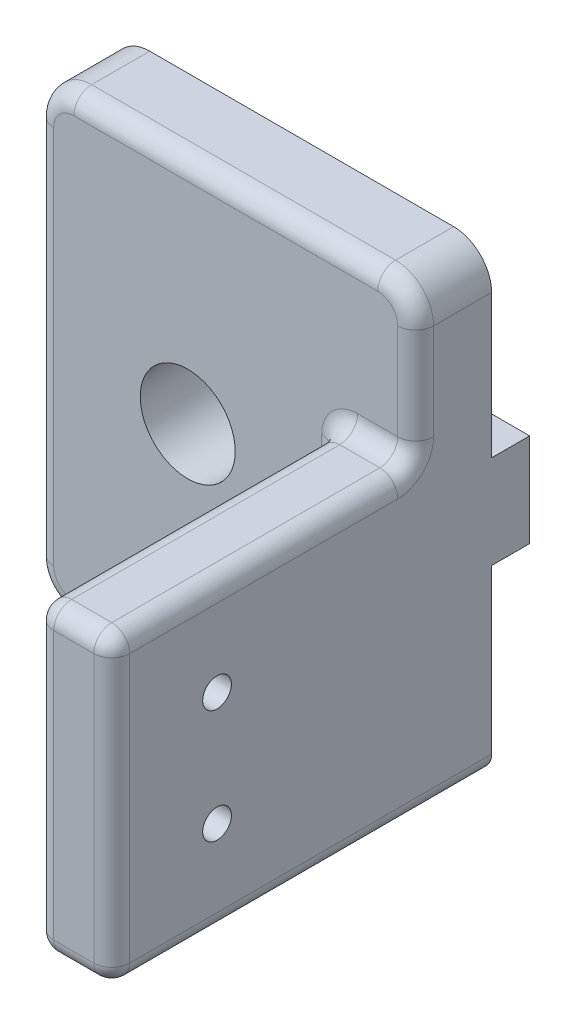
SolidWorks part; units mm, degrees
ref_plane "Front Plane" through (0, 0, 0) normal (0, 0, 1) x (1, 0, 0)
ref_plane "Top Plane" through (0, 0, 0) normal (0, 1, 0) x (1, 0, 0)
ref_plane "Right Plane" through (0, 0, 0) normal (1, 0, 0) x (0, 0, -1)
sketch "Sketch1" plane through (0, 0, 0) normal (0, 0, 1) x (1, 0, 0)
  line L1 (0, 0) -> (31.75, 0)
  line L2 (0, 0) -> (0, 38.1)
  line L3 (0, 38.1) -> (31.75, 38.1)
  line L4 (31.75, 0) -> (31.75, 38.1)
  line L5 (0, 0) -> (31.75, 38.1) construction
  line L6 (0, 38.1) -> (31.75, 0) construction
  point P4 (15.875, 19.05)
  dimension "D1" = 31.75
  dimension "D2" = 38.1
extrude "Boss-Extrude1" add sketch "Sketch1" along normal blind 6.35 contours L2 L3 L4 L1
sketch "Sketch2" plane through (0, 0, 6.35) normal (0, 0, 1) x (1, 0, 0)
  line L0 (15.875, 38.1) -> (15.875, 0) construction
  line L1 (0, 38.1) -> (31.75, 38.1) construction
  line L2 (0, 0) -> (31.75, 0) construction
  line L3 (0, 0) -> (0, 38.1) construction
  line L8 (31.75, 0) -> (25.4, 0)
  line L9 (31.75, 0) -> (31.75, 25.4)
  line L10 (31.75, 25.4) -> (25.4, 25.4)
  line L11 (25.4, 0) -> (25.4, 25.4)
  line L12 (31.75, 0) -> (25.4, 25.4) construction
  line L13 (31.75, 25.4) -> (25.4, 0) construction
  circle A0 centre (12.7, 19.05) radius 3.9688 construction
  point P8 (28.575, 17.45)
  point P13 (28.575, 12.7)
  point P18 (28.575, 7.95)
  dimension "D2" = 7.9375
  dimension "D1" = 19.05
  dimension "D3" = 25.4
  dimension "D4" = 12.7
  dimension "D5" = 6.35
  dimension "D6" = 7.95
  dimension "D7" = 9.5
extrude "Boss-Extrude2" add sketch "Sketch2" along normal blind 25.4 contours L11 L10 L9 L8
sketch "Sketch3" plane through (25.4, 0, 0) normal (-1, 0, 0) x (0, 0, 1)
  line L0 (31.75, 0) -> (6.35, 0) construction
  line L1 (31.75, 0) -> (31.75, 25.4) construction
  circle A0 centre (22.95, 17.45) radius 1.2
  circle A1 centre (22.95, 7.95) radius 1.2
  dimension "D2" = 2.4
  dimension "D1" = 9.5
  dimension "D3" = 7.95
  dimension "D4" = 8.8
extrude "Cut-Extrude1" cut sketch "Sketch3" against normal through all contours A0
sketch "Sketch4" plane through (0, 0, 6.35) normal (0, 0, 1) x (1, 0, 0)
  line L0 (0, 0) -> (0, 38.1) construction
  line L1 (0, 0) -> (25.4, 0) construction
  circle A0 centre (12.7, 19.05) radius 3.9688
  dimension "D1" = 7.9375
  dimension "D2" = 12.7
  dimension "D3" = 19.05
extrude "Cut-Extrude2" cut sketch "Sketch4" against normal through all
sketch "Sketch5" plane through (0, 0, 0) normal (-1, 0, 0) x (0, 0, 1)
  line L0 (0, 0) -> (0, 38.1) construction
  line L1 (0, 0) -> (0, 38.1)
  line L3 (0, 22.95) -> (-3.18, 22.95)
  line L4 (0, 22.95) -> (0, 15.15)
  line L5 (0, 15.15) -> (-3.18, 15.15)
  line L6 (-3.18, 22.95) -> (-3.18, 15.15)
  line L7 (0, 22.95) -> (-3.18, 15.15) construction
  line L8 (0, 15.15) -> (-3.18, 22.95) construction
  point P6 (-1.59, 19.05)
  dimension "D1" = 7.8
  dimension "D2" = 3.18
  dimension "D3" = 19.05
extrude "Boss-Extrude3" add sketch "Sketch5" against normal up to surface (31.75 mm away) contours L3 L6 L5 L1 up to face at (31.75, 17.45, 24.15)
fillet "Fillet1" radius 3.175 3 edges at (31.75, 38.1, 3.175) (0, 38.1, 3.175) (0, 0, 3.175)
fillet "Fillet2" radius 1.5 17 edges at (25.4, 0, 19.05) (14.2875, 0, 6.35) (0.9299, 0.9299, 6.35) (0, 19.05, 6.35) (0.9299, 37.1701, 6.35) (15.875, 38.1, 6.35) (30.8201, 37.1701, 6.35) (31.75, 30.1625, 6.35) (28.575, 25.4, 6.35) (25.4, 12.7, 31.75) (31.75, 12.7, 31.75) (31.75, 0, 15.875) (28.575, 0, 31.75) (25.4, 12.7, 6.35) (28.575, 25.4, 31.75) (31.75, 25.4, 19.05) (25.4, 25.4, 19.05)
sketch "Sketch6" plane through (0, 0, 0) normal (0, 0, 1) x (1, 0, 0)
  line L2 (13.4355, 22.95) -> (11.9645, 22.95)
  line L3 (11.9645, 15.15) -> (13.4355, 15.15)
  line L4 (13.4355, 22.95) -> (11.9645, 22.95)
  line L5 (11.9645, 15.15) -> (13.4355, 15.15)
  arc A2 (11.9645, 22.95) -> (11.9645, 15.15) centre (12.7, 19.05) ccw
  arc A3 (13.4355, 15.15) -> (13.4355, 22.95) centre (12.7, 19.05) ccw
  arc A4 (11.9645, 22.95) -> (11.9645, 15.15) centre (12.7, 19.05) ccw
  arc A5 (13.4355, 15.15) -> (13.4355, 22.95) centre (12.7, 19.05) ccw
  dimension "D1" = 0
extrude "Cut-Extrude3" cut sketch "Sketch6" against normal through all
sketch "Sketch7" plane through (0, 0, 0) normal (0, 0, -1) x (-1, 0, 0)
  arc A0 (-13.4355, 22.95) -> (-13.4355, 15.15) centre (-12.7, 19.05) ccw construction
  arc A1 (-13.4355, 22.95) -> (-13.4355, 15.15) centre (-12.7, 19.05) ccw construction
  circle A2 centre (-12.7, 19.05) radius 5.8663
  dimension "D1" = 11.7326
extrude "Cut-Extrude4" cut sketch "Sketch7" along normal up to next contours A2
